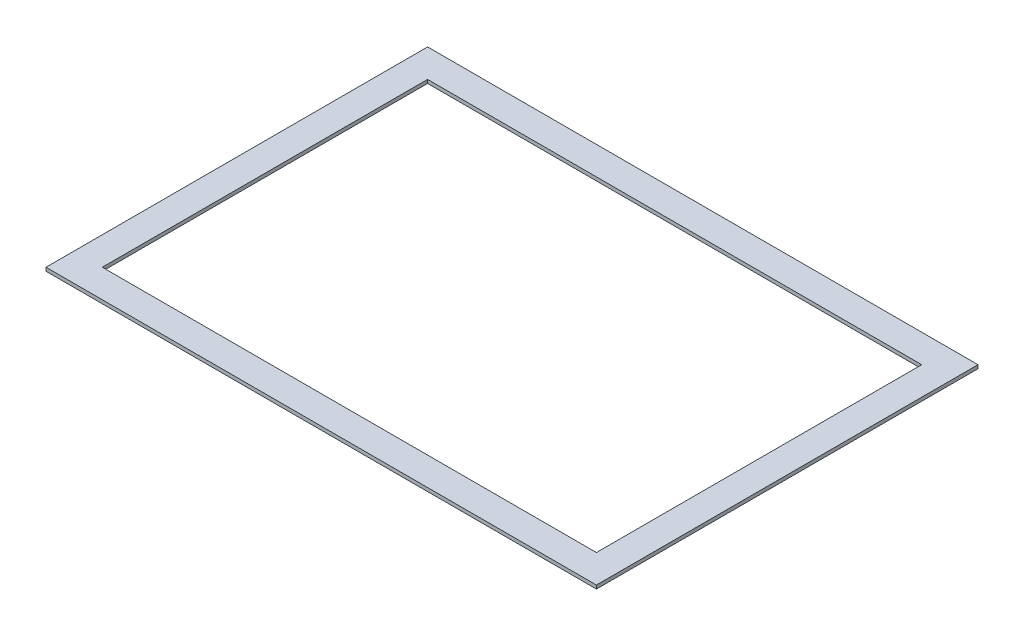
SolidWorks part; units mm, degrees
material "Silicon Rubber"
ref_plane "Front Plane" through (0, 0, 0) normal (0, 0, 1) x (1, 0, 0)
ref_plane "Top Plane" through (0, 0, 0) normal (0, 1, 0) x (1, 0, 0)
ref_plane "Right Plane" through (0, 0, 0) normal (1, 0, 0) x (0, 0, -1)
sketch "Sketch1" plane through (0, 0, 0) normal (0, 1, 0) x (1, 0, 0)
  line L0 (-223.0437, 146.8438) -> (223.0438, 146.8438)
  line L1 (-248.4437, -172.2438) -> (248.4438, -172.2438)
  line L2 (-248.4437, -172.2438) -> (-248.4437, 172.2438)
  line L3 (-248.4437, 172.2438) -> (248.4438, 172.2438)
  line L4 (248.4438, -172.2438) -> (248.4438, 172.2438)
  line L5 (-248.4437, -172.2438) -> (248.4438, 172.2438) construction
  line L6 (-248.4437, 172.2438) -> (248.4438, -172.2438) construction
  line L7 (223.0438, -146.8438) -> (223.0438, 146.8438)
  line L8 (-223.0437, -146.8438) -> (223.0438, -146.8438)
  line L9 (-223.0437, -146.8438) -> (-223.0437, 146.8438)
  point P0 (0, 0)
  dimension "D1" = 344.4875
  dimension "D2" = 496.8875
  dimension "D3" = 25.4
extrude "Boss-Extrude1" add sketch "Sketch1" along normal blind 3.175
